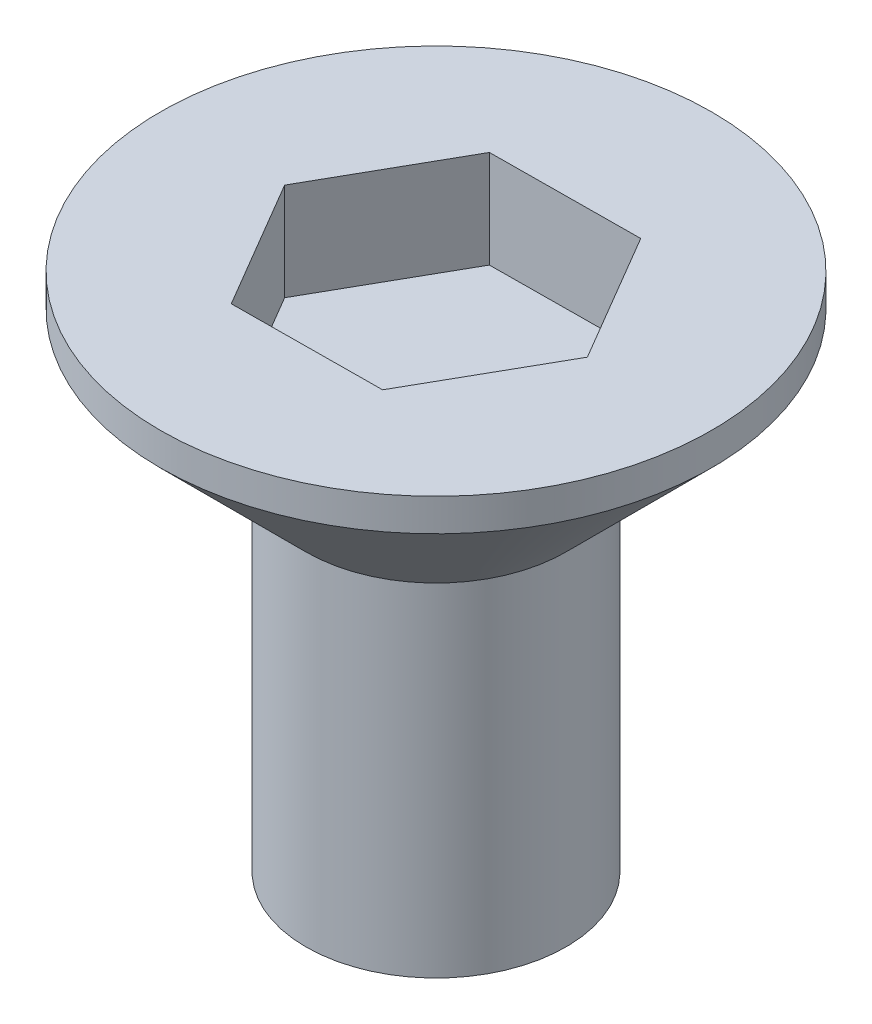
SolidWorks part; units mm, degrees
ref_plane "Спереди" through (0, 0, 0) normal (0, 0, 1) x (1, 0, 0)
ref_plane "Сверху" through (0, 0, 0) normal (0, 1, 0) x (1, 0, 0)
ref_plane "Справа" through (0, 0, 0) normal (1, 0, 0) x (0, 0, -1)
sketch "Эскиз1" plane through (0, 0, 0) normal (0, 0, 1) x (1, 0, 0)
  line L0 (0, 0) -> (4, 0)
  line L1 (4, 0) -> (4, 10.5194)
  line L2 (4, 10.5194) -> (8.4806, 15)
  line L3 (8.4806, 15) -> (8.4806, 16)
  line L4 (8.4806, 16) -> (0, 16)
  line L5 (0, 68.6446) -> (0, -29.1082) construction
  line L6 (0, 0) -> (0, 16)
revolve "Повернуть1" add sketch "Эскиз1" angle 360 about L5
sketch "Эскиз2" plane through (0, 16, 0) normal (0, 1, 0) x (1, 0, 0)
  line L1 (2.3404, -3.982) -> (4.6187, 0.0358)
  line L2 (4.6187, 0.0358) -> (2.2783, 4.0178)
  line L3 (2.2783, 4.0178) -> (-2.3404, 3.982)
  line L4 (-2.3404, 3.982) -> (-4.6187, -0.0358)
  line L5 (-4.6187, -0.0358) -> (-2.2783, -4.0178)
  line L6 (-2.2783, -4.0178) -> (2.3404, -3.982)
  circle A0 centre (0, 0) radius 4 construction
extrude "Вырез-Вытянуть1" cut sketch "Эскиз2" against normal blind 3
